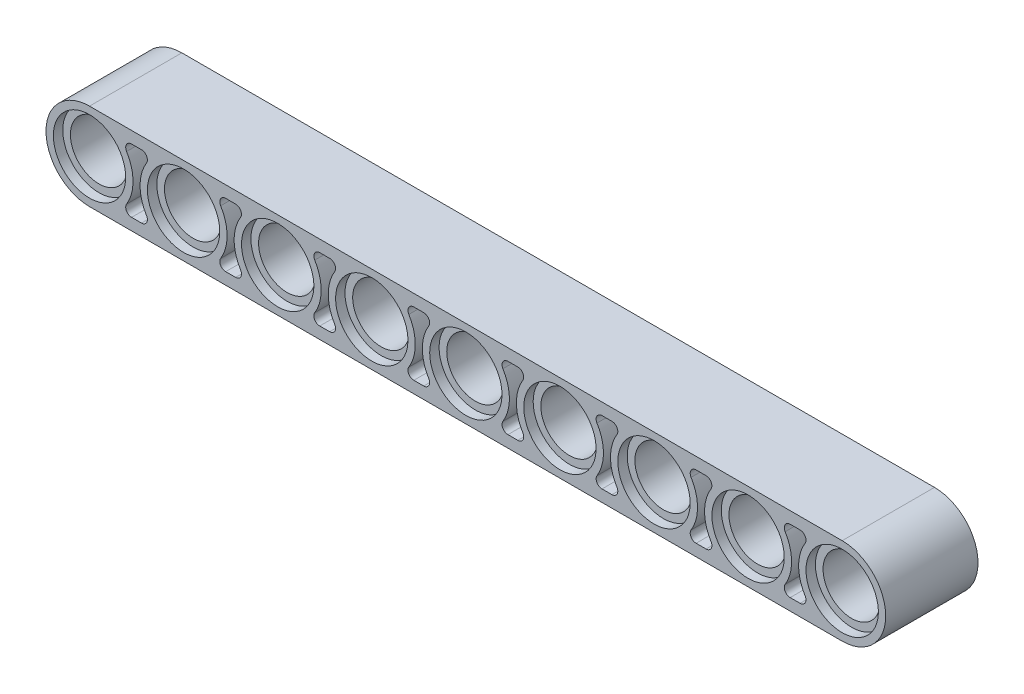
SolidWorks part; units mm, degrees
material "ABS"
ref_plane "Zero X (Front)" through (0, 0, 0) normal (0, 0, 1) x (1, 0, 0)
ref_plane "Zero Z (Top)" through (0, 0, 0) normal (0, 1, 0) x (1, 0, 0)
ref_plane "Zero Y(Right)" through (0, 0, 0) normal (1, 0, 0) x (0, 0, -1)
sketch "Sketch1" plane through (0, 0, 0) normal (0, 1, 0) x (1, 0, 0)
  line L0 (0, 2.425) -> (0, -2.425) construction
  line L1 (-3.7, 3.925) -> (-3.7, -3.925)
  line L2 (-3.7, -3.925) -> (-3.075, -3.925)
  line L3 (-3.075, -3.925) -> (-3.075, -3.125)
  line L4 (-3.075, -3.125) -> (-2.425, -3.125)
  line L5 (-2.425, -3.125) -> (-2.425, 3.125)
  line L6 (-2.425, 3.125) -> (-3.075, 3.125)
  line L7 (-3.075, 3.125) -> (-3.075, 3.925)
  line L8 (-3.075, 3.925) -> (-3.7, 3.925)
  line L9 (-1.7975, 0) -> (1.7975, 0) construction
  circle A0 centre (0, 0) radius 2.425 construction
  dimension "D1" = 4.85
  dimension "D2" = 7.85
  dimension "D3" = 7.4
  dimension "D4" = 6.25
  dimension "D5" = 6.15
revolve "Revolve1" add sketch "Sketch1" angle 360 about L0
sketch "Sketch2" plane through (0, 0, 3.925) normal (0, 0, 1) x (1, 0, 0)
  line L0 (0, 3.7) -> (-8, 3.7)
  line L1 (-1.7975, 0) -> (1.7975, 0) construction
  line L2 (-8, 3.7) -> (-8, 3.2)
  line L3 (0, -3.7) -> (-8, -3.7)
  line L4 (-3.5777, -2.7) -> (-4.4223, -2.7)
  line L5 (-3.5777, 2.7) -> (-4.4223, 2.7)
  line L6 (0, 0) -> (-8, 0) construction
  line L7 (-8, -3.2) -> (-8, -3.7)
  line L8 (0, 3.7) -> (0, 3.2)
  line L9 (0, -3.2) -> (0, -3.7)
  circle A0 centre (0, 0) radius 3.7 construction
  arc A1 (-3.1518, 1.9381) -> (-3.1518, -1.9381) centre (0, 0) ccw
  arc A2 (-4.8482, -1.9381) -> (-4.8482, 1.9381) centre (-8, 0) ccw
  arc A3 (-3.1518, -1.9381) -> (-3.5777, -2.7) centre (-3.5777, -2.2) cw
  arc A4 (-4.8482, 1.9381) -> (-4.4223, 2.7) centre (-4.4223, 2.2) cw
  arc A5 (-4.8482, -1.9381) -> (-4.4223, -2.7) centre (-4.4223, -2.2) ccw
  arc A6 (-3.5777, 2.7) -> (-3.1518, 1.9381) centre (-3.5777, 2.2) cw
  arc A7 (-8, -3.2) -> (-8, 3.2) centre (-8, 0) ccw
  arc A12 (0, 3.2) -> (0, -3.2) centre (0, 0) ccw
  dimension "D2" = 0.5
  dimension "D3" = 0.5
  dimension "D1" = 1
extrude "Boss-Extrude1" add sketch "Sketch2" against normal up to surface (7.85 mm away) up to face at (-3.7, 0, -3.925)
sketch "Sketch3" plane through (0, 0, 0) normal (0, 0, 1) x (1, 0, 0)
  line L0 (-3.5777, 2.7) -> (-4.4223, 2.7) construction
  line L1 (-3.5777, -2.7) -> (-4.4223, -2.7) construction
  line L2 (-3.5777, 2.7) -> (-4.4223, 2.7)
  line L3 (-3.5777, -2.7) -> (-4.4223, -2.7)
  arc A0 (-4.8482, -1.9381) -> (-4.8482, 1.9381) centre (-8, 0) ccw construction
  arc A1 (-4.4223, 2.7) -> (-4.8482, 1.9381) centre (-4.4223, 2.2) ccw construction
  arc A2 (-3.1518, 1.9381) -> (-3.5777, 2.7) centre (-3.5777, 2.2) ccw construction
  arc A3 (-3.5777, -2.7) -> (-3.1518, -1.9381) centre (-3.5777, -2.2) ccw construction
  arc A4 (-4.8482, -1.9381) -> (-4.4223, -2.7) centre (-4.4223, -2.2) ccw construction
  arc A6 (-4.8482, -1.9381) -> (-4.8482, 1.9381) centre (-8, 0) ccw
  arc A7 (-4.4223, 2.7) -> (-4.8482, 1.9381) centre (-4.4223, 2.2) ccw
  arc A8 (-3.1518, 1.9381) -> (-3.5777, 2.7) centre (-3.5777, 2.2) ccw
  arc A9 (-3.5777, -2.7) -> (-3.1518, -1.9381) centre (-3.5777, -2.2) ccw
  arc A10 (-4.8482, -1.9381) -> (-4.4223, -2.7) centre (-4.4223, -2.2) ccw
  arc A11 (-3.1518, 1.9381) -> (-3.1518, -1.9381) centre (0, 0) ccw construction
  arc A12 (-3.1518, 1.9381) -> (-3.1518, -1.9381) centre (0, 0) ccw
extrude "Boss-Extrude2" add sketch "Sketch3" along normal mid plane 1.2
pattern_linear "LPattern1" count 9 spacing 8 along (1, 0, 0) of "Revolve1", "Boss-Extrude1", "Boss-Extrude2"
sketch "Sketch4" plane through (0, 0, 3.925) normal (0, 0, 1) x (1, 0, 0)
  line L0 (64, 3.7) -> (-8, 3.7) construction
  line L1 (-8, -3.7) -> (64, -3.7) construction
  line L2 (0, 3.7) -> (-8, 3.7)
  line L3 (-8, -3.7) -> (0, -3.7)
  line L4 (-8, -3.2) -> (-8, -3.7) construction
  line L5 (-8, 3.7) -> (-8, -3.7)
  arc A0 (-3.1518, 1.9381) -> (-3.1518, -1.9381) centre (0, 0) ccw construction
  arc A1 (0, 3.7) -> (0, -3.7) centre (0, 0) ccw
extrude "Cut-Extrude1" cut sketch "Sketch4" against normal through all
